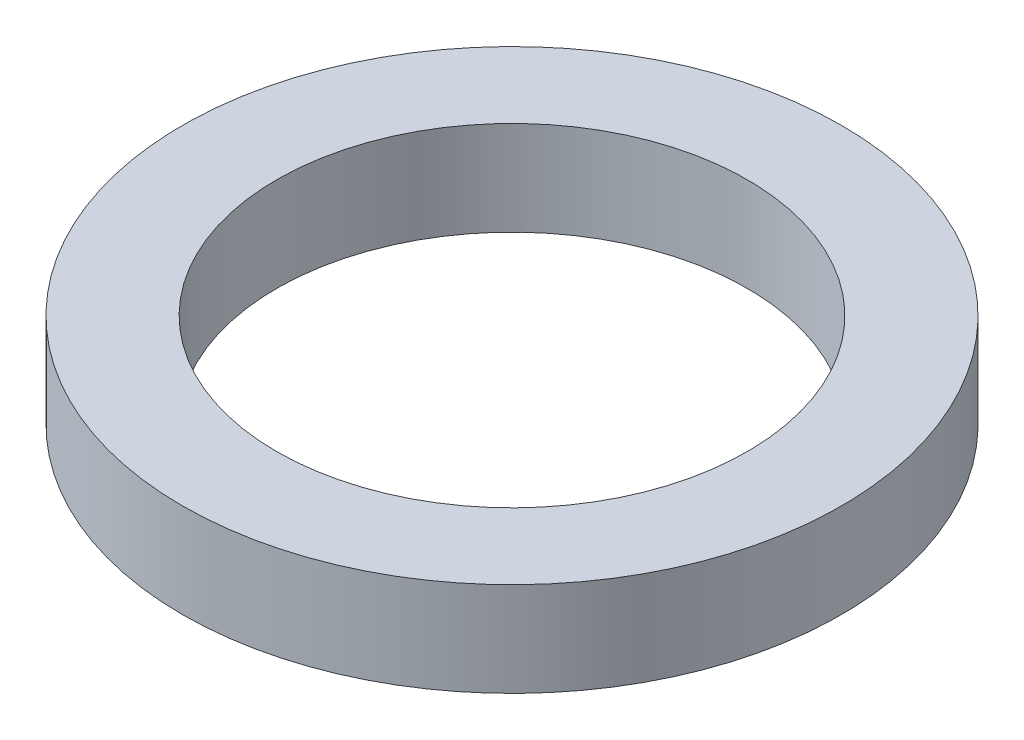
SolidWorks part; units mm, degrees
material "Brass"
ref_plane "Front Plane" through (0, 0, 0) normal (0, 0, 1) x (1, 0, 0)
ref_plane "Top Plane" through (0, 0, 0) normal (0, 1, 0) x (1, 0, 0)
ref_plane "Right Plane" through (0, 0, 0) normal (1, 0, 0) x (0, 0, -1)
sketch "Sketch1" plane through (0, 0, 0) normal (0, 1, 0) x (1, 0, 0)
  circle A0 centre (0, 0) radius 1.75
  circle A1 centre (0, 0) radius 1.25
  dimension "D1" = 0.5
  dimension "D2" = 2.5
extrude "Boss-Extrude1" add sketch "Sketch1" along normal blind 0.5
